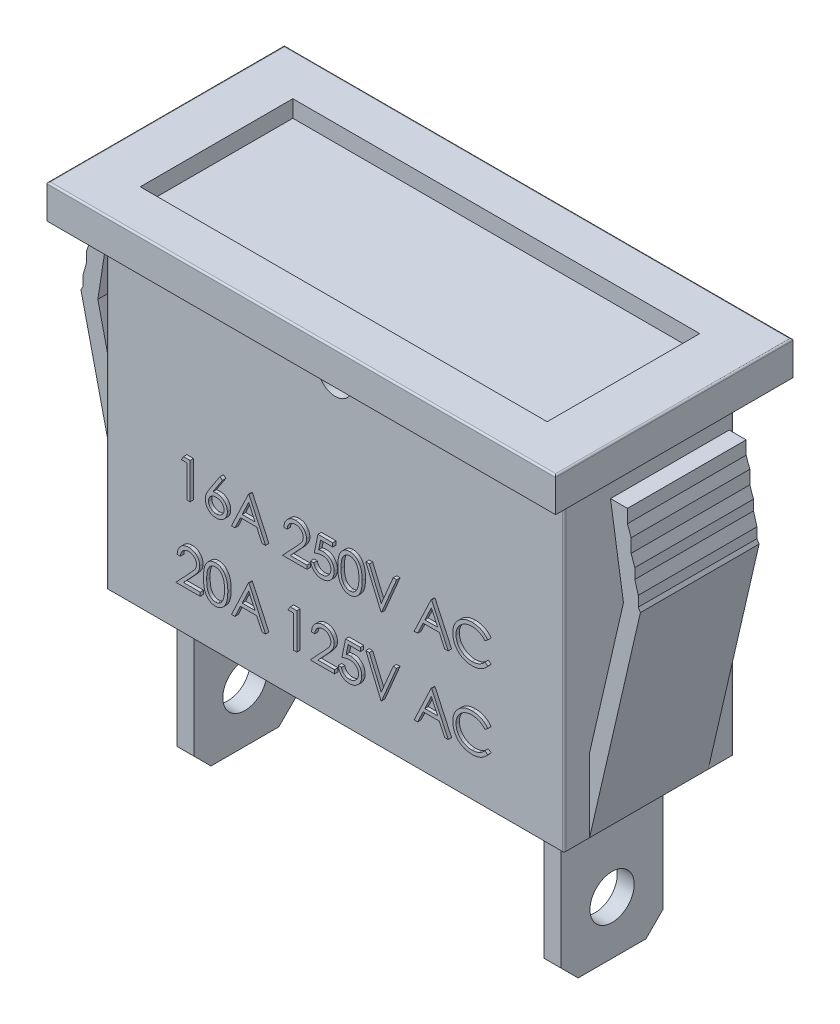
SolidWorks part; units mm, degrees
ref_plane "Front Plane" through (0, 0, 0) normal (0, 0, 1) x (1, 0, 0)
ref_plane "Top Plane" through (0, 0, 0) normal (0, 1, 0) x (1, 0, 0)
ref_plane "Right Plane" through (0, 0, 0) normal (1, 0, 0) x (0, 0, -1)
sketch "Sketch1" plane through (0, 0, 0) normal (0, 0, 1) x (1, 0, 0)
  line L0 (-13.5, 8.5) -> (-15, 8.5)
  line L1 (-15, 10.5) -> (15, 10.5)
  line L2 (-15, 10.5) -> (-15, 8.5)
  line L3 (-13.5, -10.5) -> (13.5, -10.5)
  line L4 (15, 10.5) -> (15, 8.5)
  line L5 (-13.5, -10.5) -> (13.5, -10.5)
  line L6 (-13.5, -6.1667) -> (-13.5, 8.5)
  line L8 (13.5, -6.1667) -> (13.5, 8.5)
  line L9 (-15, 8.5) -> (-13.5, 8.5)
  line L10 (13.5, 8.5) -> (15, 8.5)
  line L11 (0, 18.3113) -> (0, 10.5) construction
  line L13 (13.5, -10.5) -> (16.5, 2.5)
  line L14 (16.5, 2.5) -> (15.7358, 7.4434)
  line L15 (15.7358, 7.4434) -> (14.7358, 7.4434)
  line L16 (14.7358, 7.4434) -> (15.5, 2.5)
  line L17 (15.5, 2.5) -> (13.5, -6.1667)
  line L18 (-13.5, -10.5) -> (-16.5, 2.5)
  line L19 (-15.5, 2.5) -> (-13.5, -6.1667)
  line L20 (-16.5, 2.5) -> (-15.7358, 7.4434)
  line L21 (-14.7358, 7.4434) -> (-15.5, 2.5)
  line L22 (-15.7358, 7.4434) -> (-14.7358, 7.4434)
  line L24 (0, -10.5) -> (0, -18.3113) construction
  point P0 (0, 0)
  dimension "D1" = 30
  dimension "D3" = 1.5
  dimension "D4" = 1.5
  dimension "D5" = 3
  dimension "D6" = 1
extrude "Boss-Extrude1" add sketch "Sketch1" along normal mid plane 7 contours L22 L20 L18 L3 L13 L14 L15 L16 L17 L8 L10 L4 L1 L2 L0 L6 L19 L21
sketch "Sketch3" plane through (0, 0, 0) normal (0, 0, 1) x (1, 0, 0)
  line L1 (-13.5, 8.5) -> (13.5, 8.5)
  line L2 (-13.5, 8.5) -> (-13.5, -10.5)
  line L3 (-13.5, -10.5) -> (13.5, -10.5)
  line L4 (13.5, 8.5) -> (13.5, -10.5)
extrude "Boss-Extrude2" add sketch "Sketch3" along normal mid plane 10
sketch "Sketch4" plane through (0, 0, 0) normal (0, 0, 1) x (1, 0, 0)
  line L1 (-15, 10.5) -> (15, 10.5)
  line L2 (-15, 10.5) -> (-15, 8.5)
  line L3 (-15, 8.5) -> (15, 8.5)
  line L4 (15, 10.5) -> (15, 8.5)
extrude "Boss-Extrude3" add sketch "Sketch4" along normal mid plane 14
sketch "Sketch5" plane through (0, 10.5, 0) normal (0, 1, 0) x (1, 0, 0)
  line L1 (-12, 4.5) -> (12, 4.5)
  line L2 (-12, 4.5) -> (-12, -4.5)
  line L3 (-12, -4.5) -> (12, -4.5)
  line L4 (12, 4.5) -> (12, -4.5)
  line L5 (-12, 4.5) -> (12, -4.5) construction
  line L6 (-12, -4.5) -> (12, 4.5) construction
  point P0 (0, 0)
  dimension "D1" = 24
  dimension "D2" = 9
extrude "Cut-Extrude1" cut sketch "Sketch5" against normal blind 1
sketch "Sketch6" plane through (0, -10.5, 0) normal (0, -1, 0) x (1, 0, 0)
  line L1 (-11.3277, 3) -> (-10.3277, 3)
  line L2 (-11.3277, 3) -> (-11.3277, -3)
  line L3 (-11.3277, -3) -> (-10.3277, -3)
  line L4 (-10.3277, 3) -> (-10.3277, -3)
  line L5 (-11.3277, 3) -> (-10.3277, -3) construction
  line L6 (-11.3277, -3) -> (-10.3277, 3) construction
  line L8 (13.5, -5) -> (-13.5, -5) construction
  line L9 (0, 2.6656) -> (0, -4.4759) construction
  line L10 (11.3277, -3) -> (10.3277, 3) construction
  line L11 (11.3277, 3) -> (10.3277, -3) construction
  line L12 (10.3277, 3) -> (10.3277, -3)
  line L13 (11.3277, -3) -> (10.3277, -3)
  line L14 (11.3277, 3) -> (11.3277, -3)
  line L15 (11.3277, 3) -> (10.3277, 3)
  point P0 (-10.8277, 0)
  point P14 (10.8277, 0)
  dimension "D1" = 1
  dimension "D2" = 6
  dimension "D3" = 5
extrude "Boss-Extrude4" add sketch "Sketch6" along normal blind 9
chamfer "Chamfer1" distance 1 angle 45 4 edges at (-10.8277, -19.5, -3) (-10.8277, -19.5, 3) (10.8277, -19.5, 3) (10.8277, -19.5, -3)
sketch "Sketch8" plane through (-11.3277, 0, 0) normal (-1, 0, 0) x (0, 0, 1)
  line L0 (3, -10.5) -> (-3, -10.5) construction
  line L1 (-1.3047, -10.5) -> (1.3047, -10.5)
  circle A0 centre (0, -16.3621) radius 1.3047
  arc A1 (-1.3047, -10.5) -> (1.3047, -10.5) centre (0, -10.5) ccw
extrude "Cut-Extrude2" cut sketch "Sketch8" against normal through all both and the other way through all
sketch "Sketch9" plane through (0, 0, 5) normal (0, 0, 1) x (1, 0, 0)
  circle A0 centre (0, 7.0407) radius 1
extrude "Cut-Extrude3" cut sketch "Sketch9" against normal through all
sketch "Sketch10" plane through (0, 0, -3.5) normal (0, 0, -1) x (-1, 0, 0)
  line L0 (-15.7358, 7.4434) -> (-15.7358, 6.6577)
  line L1 (-15.7358, 6.6577) -> (-15.9516, 6.0478)
  line L2 (-16.5, 2.5) -> (-15.7358, 7.4434) construction
  line L3 (-15.9516, 6.0478) -> (-15.9516, 5.2508)
  line L4 (-15.9516, 5.2508) -> (-16.1704, 4.6322)
  line L5 (-16.1704, 4.6322) -> (-16.1704, 4.0291)
  line L6 (-16.1704, 4.0291) -> (-16.3733, 3.3196)
  line L7 (-16.3733, 3.3196) -> (-16.3733, 2.7148)
  line L8 (-16.3733, 2.7148) -> (-16.5, 2.5)
  line L9 (-16.5, 2.5) -> (-16.7229, 2.5)
  line L10 (-16.7229, 2.5) -> (-15.8437, 7.4434)
  line L11 (-15.8437, 7.4434) -> (-15.7358, 7.4434)
  line L12 (0, 13.127) -> (0, 4.6322) construction
  line L13 (15.8437, 7.4434) -> (15.7358, 7.4434)
  line L14 (16.7229, 2.5) -> (15.8437, 7.4434)
  line L15 (16.5, 2.5) -> (16.7229, 2.5)
  line L16 (16.3733, 2.7148) -> (16.5, 2.5)
  line L17 (16.3733, 3.3196) -> (16.3733, 2.7148)
  line L18 (16.1704, 4.0291) -> (16.3733, 3.3196)
  line L19 (16.1704, 4.6322) -> (16.1704, 4.0291)
  line L20 (15.9516, 5.2508) -> (16.1704, 4.6322)
  line L21 (15.9516, 6.0478) -> (15.9516, 5.2508)
  line L22 (15.7358, 6.6577) -> (15.9516, 6.0478)
  line L23 (15.7358, 7.4434) -> (15.7358, 6.6577)
extrude "Cut-Extrude4" cut sketch "Sketch10" against normal through all
sketch "Sketch11" plane through (0, 0, 5) normal (0, 0, 1) x (1, 0, 0)
  text T0 "16A 250V AC\r\n20A 125V AC" font "Century Gothic" height in points 8
extrude "Boss-Extrude5" add sketch "Sketch11" along normal blind 0.2
fillet "Fillet1" radius 0.1 4 edges at (13.5, -1, -5) (-13.5, -1, -5) (-13.5, -1, 5) (13.5, -1, 5)
fillet "Fillet5" radius 0.1 4 edges at (0, 10.5, -7) (15, 10.5, 0) (-15, 10.5, 0) (0, 10.5, 7)
